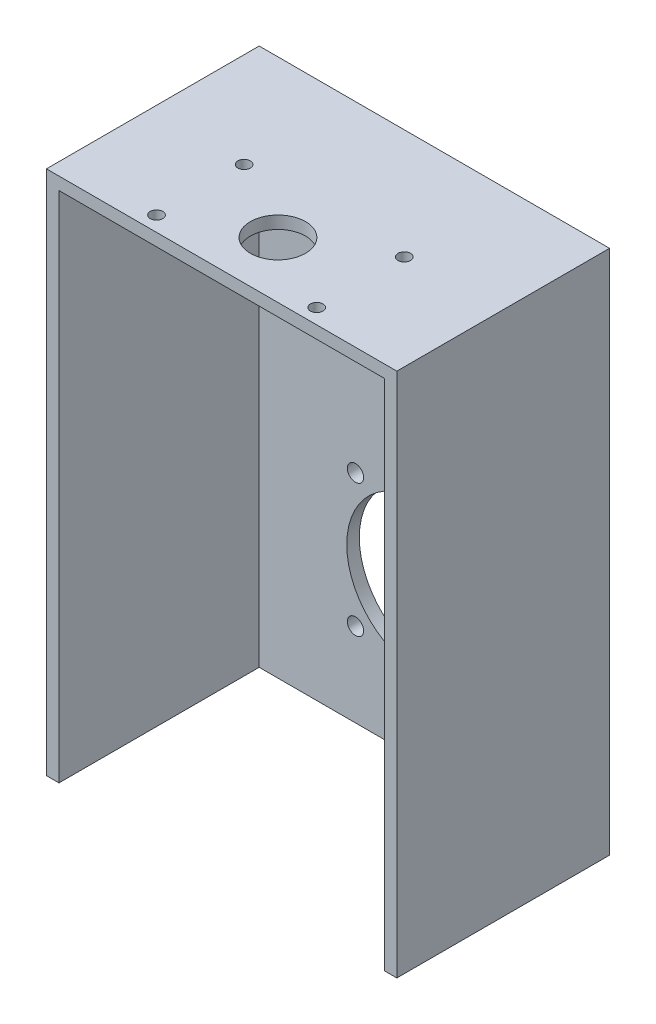
SolidWorks part; units mm, degrees
ref_plane "前视基准面" through (0, 0, 0) normal (0, 0, 1) x (1, 0, 0)
ref_plane "上视基准面" through (0, 0, 0) normal (0, 1, 0) x (1, 0, 0)
ref_plane "右视基准面" through (0, 0, 0) normal (1, 0, 0) x (0, 0, -1)
sketch "草图1" plane through (0, 0, 0) normal (0, 1, 0) x (1, 0, 0)
  circle A0 centre (0, 0) radius 13
  dimension "D1" = 26
extrude "凸台-拉伸1" add sketch "草图1" along normal blind 20
sketch "草图2" plane through (0, 20, 0) normal (0, 1, 0) x (1, 0, 0)
  circle A0 centre (0, 0) radius 13
  dimension "D1" = 26
extrude "凸台-拉伸2" add sketch "草图2" along normal blind 400
sketch "草图3" plane through (0, 420, 0) normal (0, 1, 0) x (1, 0, 0)
  circle A0 centre (0, 0) radius 11
  dimension "D1" = 22
sketch "草图4" plane through (0, 0, 0) normal (0, -1, 0) x (1, 0, 0)
  line L1 (-70, 22.5) -> (70, 22.5)
  line L2 (-70, 22.5) -> (-70, -62.5)
  line L3 (-70, -62.5) -> (70, -62.5)
  line L4 (70, 22.5) -> (70, -62.5)
  line L5 (-70, 22.5) -> (70, -62.5) construction
  line L6 (-70, -62.5) -> (70, 22.5) construction
  point P8 (0, -20)
  dimension "D1" = 140
  dimension "D2" = 85
  dimension "D3" = 20
extrude "凸台-拉伸3" add sketch "草图4" along normal blind 210 separate body
shell "抽壳2" thickness 5
sketch "草图5" plane through (0, 0, 22.5) normal (0, 0, 1) x (1, 0, 0)
  line L0 (70, -210) -> (-70, -210) construction
  line L1 (65, -205) -> (-65, -205)
  line L2 (65, -205) -> (65, -210)
  line L3 (65, -210) -> (-65, -210)
  line L4 (-65, -205) -> (-65, -210)
  line L5 (-65, -205) -> (-65, -5) construction
extrude "切除-拉伸3" cut sketch "草图5" against normal up to surface (80 mm away) up to face at (0, -105, -57.5)
sketch "草图6" plane through (0, 0, -62.5) normal (0, 0, -1) x (-1, 0, 0)
  line L1 (0, -150) -> (82.393, -67.607) construction
  circle A0 centre (0, -150) radius 30
  circle A1 centre (26.5165, -123.4835) radius 3.25
  circle A2 centre (26.5165, -176.5165) radius 3.25
  circle A3 centre (-26.5165, -176.5165) radius 3.25
  circle A4 centre (-26.5165, -123.4835) radius 3.25
  point P21 (0, -150)
  dimension "D1" = 60
  dimension "D5" = 6.5
  dimension "D2" = 150
  dimension "D4" = 37.5
  dimension "D6" = 4
extrude "切除-拉伸4" cut sketch "草图6" against normal blind 10
extrude "切除-拉伸5" cut sketch "草图3" against normal up to surface (425 mm away) up to face at (0, -5, -17.5)
sketch "草图7" plane through (0, 420, 0) normal (0, 1, 0) x (1, 0, 0)
  circle A1 centre (0, 0) radius 13
  circle A2 centre (0, 0) radius 13
  dimension "D1" = 0
extrude "切除-拉伸6" cut sketch "草图7" against normal up to surface (420 mm away) up to face at (0, 0, -11)
sketch "草图8" plane through (0, 0, 0) normal (0, 1, 0) x (1, 0, 0)
  circle A0 centre (-32.0209, -16.5) radius 2.5 construction
  circle A1 centre (-32.0209, 18.5) radius 2.5 construction
  circle A2 centre (31.9791, -16.5) radius 2.5 construction
  circle A3 centre (31.9791, 18.5) radius 2.5 construction
  circle A4 centre (-32.0209, -16.5) radius 2.5
  circle A5 centre (-32.0209, 18.5) radius 2.5
  circle A6 centre (31.9791, -16.5) radius 2.5
  circle A7 centre (31.9791, 18.5) radius 2.5
extrude "切除-拉伸7" cut sketch "草图8" against normal blind 5
